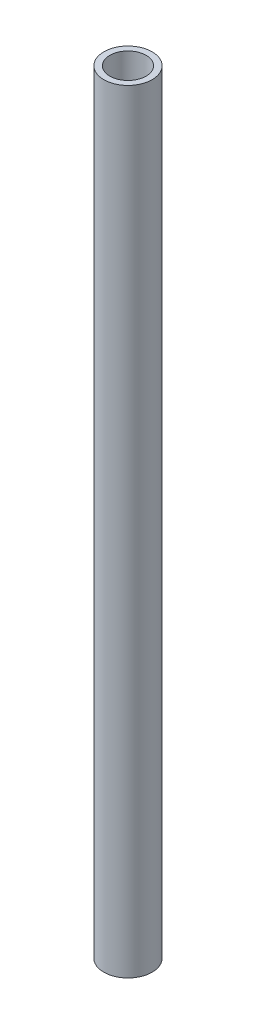
SolidWorks part; units mm, degrees
ref_plane "Front Plane" through (0, 0, 0) normal (0, 0, 1) x (1, 0, 0)
ref_plane "Top Plane" through (0, 0, 0) normal (0, 1, 0) x (1, 0, 0)
ref_plane "Right Plane" through (0, 0, 0) normal (1, 0, 0) x (0, 0, -1)
sketch "Sketch1" plane through (0, 0, 0) normal (0, 1, 0) x (1, 0, 0)
  circle A0 centre (-391.1817, 212.7433) radius 12.7
  circle A1 centre (-391.1817, 212.7433) radius 9.525
  dimension "D1" = 19.05
  dimension "D2" = 25.4
extrude "Boss-Extrude2" add sketch "Sketch1" along normal blind 406.4
